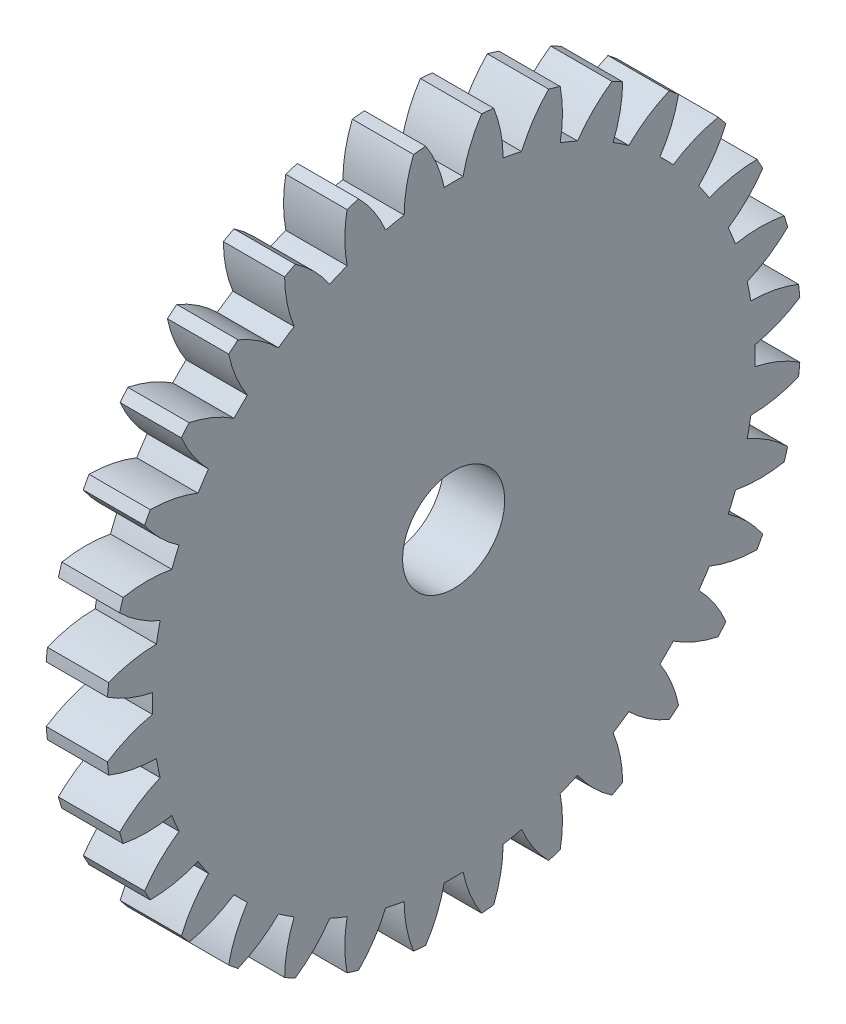
SolidWorks part; units mm, degrees
ref_plane "Plane1" through (0, 0, 0) normal (0, 0, 1) x (1, 0, 0)
ref_plane "Plane2" through (0, 0, 0) normal (0, 1, 0) x (1, 0, 0)
ref_plane "Plane3" through (0, 0, 0) normal (1, 0, 0) x (0, 0, -1)
other "Configuration Table"
sketch "HoldingSke" plane through (0, 0, 0) normal (0, 1, 0) x (1, 0, 0)
  line L0 (0, 0) -> (0.848, -0.5299)
  line L1 (-15, 0) -> (100, 0) construction
  line L2 (0, 0) -> (-2.1039, 2.3779)
  line L3 (0, 0) -> (-11.863, 4.5341)
  line L4 (0, 0) -> (7.3237, 4.5764)
  line L5 (0, 0) -> (-46.8476, -17.4728)
  line L6 (0, 0) -> (-2.4869, -1.6779)
  line L7 (-2.1039, 2.3779) -> (8.6586, 51.2059)
  line L8 (-76.2, 54.61) -> (-75.3, 54.61)
  line L9 (-71.009, 38.7566) -> (-53.1078, 45.2721)
  line L10 (-76.2, 71.12) -> (104.1128, 71.12)
  line L11 (0, 0) -> (-3, 0)
  line L12 (-76.2, 101.6) -> (-76.162, 101.6)
  line L13 (24.9733, 27.94) -> (52.9518, 28.4284)
  line L14 (24.9733, 27.94) -> (24.9743, 27.94)
  line L15 (24.9733, 27.94) -> (100.4006, 29.5858)
  line L16 (-63.627, -1) -> (-12.827, -1)
  circle A0 centre (0, 0) radius 2.5
  circle A1 centre (0, 0) radius 14.749
  circle A2 centre (0, 0) radius 37.5
  circle A3 centre (0, 0) radius 2.5
  dimension "MHD" = 29.498
  dimension "Hub_dia" = 75
  dimension "Bore" = 5
  dimension "MBD" = 5
  dimension "Num_teeth" = 32
  dimension "Pitch" = 1
  dimension "Overall_len" = 50
  dimension "Show_teeth" = 32
  dimension "Thickness" = 3
  dimension "OAL" = 50.0001
  dimension "T_dim" = 0.9
  dimension "Ap" = 20
  dimension "H" = 19.05
  dimension "Pitch_radius" = 180.3128
  dimension "Width" = 3
  dimension "Backlash" = 0.038
  dimension "Addendum_fac" = 1
  dimension "Dedendum_fac" = 1.25
  dimension "Clearance_fac" = 0.25
  dimension "Dedendum_add" = 0.001
  dimension "Module" = 1
sketch "BasProSke" plane through (0, 0, 0) normal (0, 1, 0) x (1, 0, 0)
  line L0 (-10, 0) -> (60, 0) construction
  line L1 (0, 0) -> (0, 17)
  line L2 (0, 0) -> (3, 0)
  line L3 (3, 0) -> (3, 17)
  line L4 (3, 17) -> (0, 17)
  dimension "Thickness" = 3
  dimension "Diameter" = 34
revolve "Base-Revolve" add sketch "BasProSke" angle 360 about L0
sketch "TooCutSke" plane through (0, 0, 0) normal (1, 0, 0) x (0, 0, -1)
  line L1 (0, 0) -> (0, 107) construction
  line L2 (0, 0) -> (-0.8516, 15.9773) construction
  line L3 (0, 0) -> (-3.1334, 31.8138) construction
  line L4 (-0.8516, 15.9773) -> (-1.5667, 15.9069) construction
  arc A0 (0.462, 14.7418) -> (-0.462, 14.7418) centre (0, 0) ccw
  arc A1 (1.3867, 16.9688) -> (-1.3867, 16.9688) centre (0, 0) ccw
  circle A2 centre (0, 0) radius 16 construction
  circle A3 centre (0, 0) radius 15.0351 construction
  arc A4 (-0.462, 14.7418) -> (-1.3867, 16.9688) centre (-6.7293, 13.4451) ccw
  arc A5 (1.3867, 16.9688) -> (0.462, 14.7418) centre (6.7293, 13.4451) ccw
  dimension "Root_dia" = 29.498
  dimension "Overcut_dia" = 34.0508
  dimension "Pitch_dia" = 32
  dimension "Base_dia" = 30.0702
  dimension "Flank_rad" = 6.4
  dimension "Half_ang" = 5.625
  dimension "Half_CT" = 0.7186
extrude "ToothCut" cut sketch "TooCutSke" along normal through all
fillet "Breaks" [suppressed] radius 0.02
fillet "RootFillets" [suppressed] radius 0.251
pattern_circular "TeethCuts" count 32 every 11.25 about axis through (-10, 0, 0) along (1, 0, 0) of "ToothCut", "RootFillets", "Breaks"
sketch "HubNeaOneSke" plane through (0, 0, 0) normal (-1, 0, 0) x (0, 0, 1)
  circle A0 centre (0, 0) radius 14.749
  dimension "Diameter" = 29.498
extrude "HubNearOne" [suppressed] add sketch "HubNeaOneSke" along normal blind 47.0001
sketch "HubNeaBotSke" plane through (0, 0, 0) normal (-1, 0, 0) x (0, 0, 1)
  circle A0 centre (0, 0) radius 14.749
  dimension "Diameter" = 29.498
extrude "HubNearBoth" [suppressed] add sketch "HubNeaBotSke" along normal blind 23.5
ref_plane "FarPln" through (3, 0, 0) normal (1, 0, 0) x (0, 0, -1)
sketch "HubFarSke" plane through (3, 0, 0) normal (1, 0, 0) x (0, 0, -1)
  circle A0 centre (0, 0) radius 14.749
  dimension "Diameter" = 29.498
extrude "HubFar" [suppressed] add sketch "HubFarSke" along normal blind 23.5
sketch "BorSke" plane through (0, 0, 0) normal (1, 0, 0) x (0, 0, -1)
  circle A0 centre (0, 0) radius 2.5
  dimension "Diameter" = 5
extrude "Bore" cut sketch "BorSke" along normal mid plane 100.0001
sketch "KeySke" plane through (0, 0, 0) normal (1, 0, 0) x (0, 0, -1)
  line L0 (-1, 0) -> (-1, 3.4)
  line L1 (-1, 3.4) -> (1, 3.4)
  line L2 (1, 3.4) -> (1, 0)
  line L3 (0, 0) -> (0, 34) construction
  line L4 (-1, 0) -> (1, 0)
  dimension "Offset" = 3.4
  dimension "Width" = 2
extrude "Keyway" [suppressed] cut sketch "KeySke" along normal mid plane 100.0001
pattern_circular "Keyway2" [suppressed] count 2 every 90 about axis through (-10, 0, 0) along (1, 0, 0)
equation "' \"Module@HoldingSke\" = 6.35"
equation "' \"Num_teeth@HoldingSke\" = 12"
equation "' \"Ap@HoldingSke\" =  20"
equation "' \"Ap@HoldingSke\" = 20"
equation "' \"Width@HoldingSke\" = 0.5 * 25.4"
equation "' \"Hub_dia@HoldingSke\"= 1 * 25.4"
equation "' \"Hub_dia@HoldingSke\" = 1 * 25.4"
equation "' \"Overall_len@HoldingSke\" = 1.0 * 25.4"
equation "' \"Bore@HoldingSke\" = 0.75 * 25.4"
equation "' \"T_dim@HoldingSke\" = 0.1 * 25.4"
equation "' \"Width@KeySke\" = 0.25 * 25.4"
equation "' \"Show_teeth@HoldingSke\" = 13"
equation "' \"Backlash@HoldingSke\" = 0.009 * 25.4"
equation "' \"Addendum_fac@HoldingSke\" = 1.0"
equation "' \"Dedendum_fac@HoldingSke\" = 1.25"
equation "' \"Dedendum_add@HoldingSke\" = 0.00005 * 25.4"
equation "' \"Clearance_fac@HoldingSke\" = 0.25"
equation "\"Pitch@HoldingSke\" = 1 / \"Module@HoldingSke\""
equation "\"Overcut_dia@TooCutSke\" = (\"Num_teeth@HoldingSke\" + 2 * \"Addendum_fac@HoldingSke\") / \"Pitch@HoldingSke\" + 0.002 * 25.4"
equation "\"Pitch_dia@TooCutSke\" = \"Num_teeth@HoldingSke\" / \"Pitch@HoldingSke\""
equation "\"Base_dia@TooCutSke\" = \"Num_teeth@HoldingSke\" / \"Pitch@HoldingSke\" * cos((\"Ap@HoldingSke\"  * 3.14159265 / 180))"
equation "\"Root_dia@TooCutSke\" = (\"Num_teeth@HoldingSke\" + 2) / \"Pitch@HoldingSke\" - 2 * (\"Addendum_fac@HoldingSke\" + \"Dedendum_fac@HoldingSke\") / \"Pitch@HoldingSke\" - \"Dedendum_add@HoldingSke\" * 2"
equation "\"Half_ang@TooCutSke\" = 180 / \"Num_teeth@HoldingSke\""
equation "\"Half_CT@TooCutSke\" = \"Num_teeth@HoldingSke\" / \"Pitch@HoldingSke\" * sin((3.14159265 / 2 / \"Num_teeth@HoldingSke\")) / 2 - 7 * \"Backlash@HoldingSke\" / 4"
equation "\"Flank_rad@TooCutSke\" = \"Num_teeth@HoldingSke\" / \"Pitch@HoldingSke\" / 5"
equation "\"Radius@RootFillets\" = \"Clearance_fac@HoldingSke\" / \"Pitch@HoldingSke\" + \"Dedendum_add@HoldingSke\""
equation "\"Break_rad@Breaks\" = 0.02 / \"Pitch@HoldingSke\""
equation "\"Thickness@HoldingSke\" = \"Width@HoldingSke\""
equation "\"OAL@HoldingSke\" = \"Thickness@HoldingSke\""
equation "\"MHD@HoldingSke\" = (\"Num_teeth@HoldingSke\" + 2) / \"Pitch@HoldingSke\" - 2 * (\"Addendum_fac@HoldingSke\" + \"Dedendum_fac@HoldingSke\")  / \"Pitch@HoldingSke\" - \"Dedendum_add@HoldingSke\" * 2"
equation "\"MBD@HoldingSke\" = (\"Num_teeth@HoldingSke\" + 2) / \"Pitch@HoldingSke\" - 2 * (\"Addendum_fac@HoldingSke\" + \"Dedendum_fac@HoldingSke\")  / \"Pitch@HoldingSke\" - \"Dedendum_add@HoldingSke\" * 2 - 0.002 * 25.4"
equation "\"MHD@HoldingSke\" = ((sgn( \"MHD@HoldingSke\" - \"Hub_dia@HoldingSke\" )-1)*( \"MHD@HoldingSke\" - \"Hub_dia@HoldingSke\" ))/-2+ \"Hub_dia@HoldingSke\""
equation "\"MBD@HoldingSke\" = ((sgn( \"MBD@HoldingSke\" - \"Bore@HoldingSke\" )-1)*( \"MBD@HoldingSke\" - \"Bore@HoldingSke\" ))/-2+ \"Bore@HoldingSke\""
equation "\"OAL@HoldingSke\" = ((sgn( \"OAL@HoldingSke\" - \"Overall_len@HoldingSke\" )+1)*( \"OAL@HoldingSke\" - \"Overall_len@HoldingSke\" ))/2 + \"Overall_len@HoldingSke\" + 0.000002 * 25.4"
equation "\"Num_teeth@TeethCuts\" = int( \"Show_teeth@HoldingSke\" ) + 1"
equation "\"Num_teeth@TeethCuts\" = ((sgn( \"Num_teeth@TeethCuts\" - \"Num_teeth@HoldingSke\" )-1)*( \"Num_teeth@TeethCuts\" - \"Num_teeth@HoldingSke\" ))/-2+ \"Num_teeth@HoldingSke\""
equation "\"Num_teeth@TeethCuts\" = ((sgn( \"Num_teeth@TeethCuts\" - 2.0)+1)*( \"Num_teeth@TeethCuts\" - 2.0))/2 +2.0"
equation "\"Angle@TeethCuts\" = 360.0 / \"Num_teeth@HoldingSke\""
equation "\"Diameter@BasProSke\" = (\"Num_teeth@HoldingSke\" + 2 * \"Addendum_fac@HoldingSke\") / \"Pitch@HoldingSke\""
equation "\"Thickness@BasProSke\"  = \"Thickness@HoldingSke\""
equation "' \"Fillet_rad@BasProSke\" =  \"Thickness@HoldingSke\" * 0.05"
equation "' \"Fillet_rad@BasProSke\" = \"Thickness@HoldingSke\" * 0.05"
equation "\"MHD@HoldingSke\" = ((sgn( \"MHD@HoldingSke\" - \"Root_dia@TooCutSke\" )-1)*( \"MHD@HoldingSke\" - \"Root_dia@TooCutSke\" ))/-2+ \"Root_dia@TooCutSke\""
equation "\"Diameter@HubNeaOneSke\" = \"MHD@HoldingSke\""
equation "\"Length@HubNearOne\" = \"OAL@HoldingSke\" - \"Thickness@BasProSke\""
equation "\"Diameter@HubNeaBotSke\" = \"MHD@HoldingSke\""
equation "\"Length@HubNearBoth\" = ( \"OAL@HoldingSke\" - \"Thickness@BasProSke\" ) / 2.0"
equation "\"Thickness@FarPln\" = \"Thickness@BasProSke\""
equation "\"Diameter@HubFarSke\" = \"MHD@HoldingSke\""
equation "\"Length@HubFar\" = ( \"OAL@HoldingSke\" - \"Thickness@BasProSke\" ) / 2.0"
equation "\"Diameter@BorSke\" = \"MBD@HoldingSke\""
equation "\"D1@Bore\" = \"OAL@HoldingSke\" * 2.0"
equation "\"D1@Keyway\" = \"OAL@HoldingSke\" * 2.0"
equation "\"Offset@KeySke\" = \"T_dim@HoldingSke\" + \"MBD@HoldingSke\" / 2.0"
